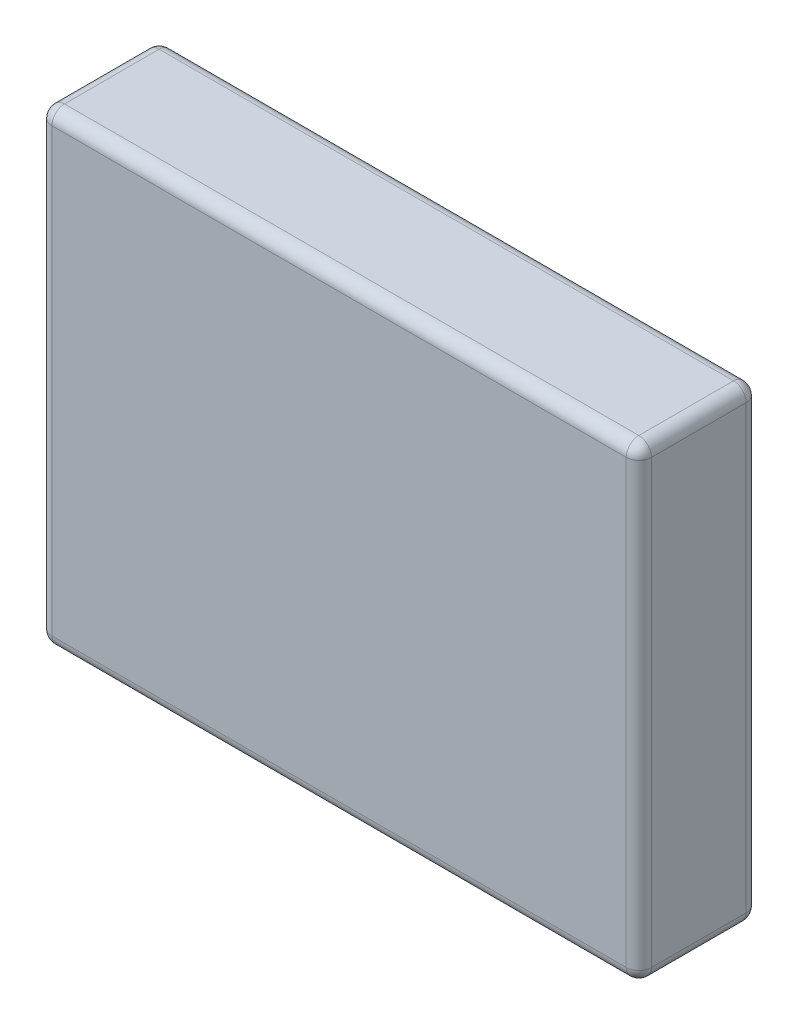
SolidWorks part; units mm, degrees
ref_plane "前视基准面" through (0, 0, 0) normal (0, 0, 1) x (1, 0, 0)
ref_plane "上视基准面" through (0, 0, 0) normal (0, 1, 0) x (1, 0, 0)
ref_plane "右视基准面" through (0, 0, 0) normal (1, 0, 0) x (0, 0, -1)
sketch "草图2" plane through (0, 0, 0) normal (0, 0, 1) x (1, 0, 0)
  line L1 (-47.5, 37) -> (47.5, 37)
  line L2 (-47.5, 37) -> (-47.5, -37)
  line L3 (-47.5, -37) -> (47.5, -37)
  line L4 (47.5, 37) -> (47.5, -37)
  dimension "D1" = 95
  dimension "D2" = 74
  dimension "D3" = 37
  dimension "D4" = 47.5
extrude "凸台-拉伸2" add sketch "草图2" along normal blind 19
fillet "圆角1" radius 2 12 edges at (-47.5, 0, 0) (0, -37, 0) (47.5, 0, 0) (0, 37, 0) (-47.5, 0, 19) (0, -37, 19) (0, 37, 19) (-47.5, 37, 9.5) (47.5, 37, 9.5) (47.5, -37, 9.5) (-47.5, -37, 9.5) (47.5, 0, 19)
